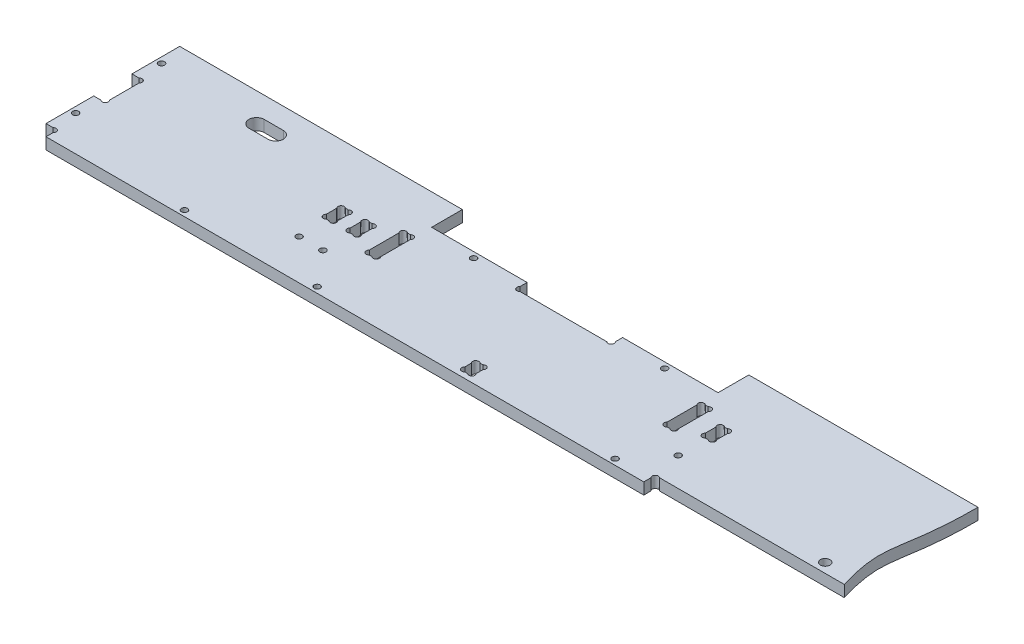
SolidWorks part; units mm, degrees
ref_plane "Plan de face" through (0, 0, 0) normal (0, 0, 1) x (1, 0, 0)
ref_plane "Plan de dessus" through (0, 0, 0) normal (0, 1, 0) x (1, 0, 0)
ref_plane "Plan de droite" through (0, 0, 0) normal (1, 0, 0) x (0, 0, -1)
sketch "Esquisse1" plane through (0, 0, 0) normal (0, 1, 0) x (1, 0, 0)
  line L0 (-13.419, 0) -> (480.5123, 0) construction
  line L1 (0, -21.3485) -> (0, 130.4665) construction
  line L2 (63.3362, 3) -> (427.6375, 3) construction
  line L3 (298, -66.9493) -> (298, 92.6945) construction
  line L4 (-13.419, 82) -> (480.5123, 82) construction
  line L5 (75.5, 6) -> (75.5, -21.3485) construction
  line L6 (457.6214, 41) -> (252.9914, 41) construction
  line L7 (300.2627, 51) -> (301.7373, 51)
  line L8 (142, 90.8171) -> (142, 7) construction
  line L9 (133, 90.8171) -> (133, -36.6843) construction
  line L10 (127, 90.8171) -> (127, 10) construction
  line L11 (109.7789, 46) -> (136.5161, 46) construction
  line L12 (-19.7637, 41) -> (137.7878, 41) construction
  line L13 (130, 28) -> (130, 5) construction
  line L14 (133, 46) -> (116.3933, 29.3933) construction
  line L15 (130.7373, 46) -> (129.2627, 46)
  line L16 (127, 43.7373) -> (127, 38.2627)
  line L17 (6, 31) -> (-11.5553, 48.5553) construction
  line L18 (6, 33.2627) -> (6, 48.7373)
  line L19 (3.7373, 31) -> (0, 31)
  line L20 (457.6214, 76) -> (-13.419, 76) construction
  line L21 (223, -7.7025) -> (223, 120.8663) construction
  line L22 (148, 59.9) -> (198, 59.9)
  line L23 (129.2627, 36) -> (130.7373, 36)
  line L24 (133, 38.2627) -> (133, 43.7373)
  line L25 (112.072, 21) -> (136.5161, 21) construction
  line L26 (313, 38.2627) -> (313, 43.7373)
  line L27 (304, -66.9493) -> (304, 92.6945) construction
  line L28 (266.0575, 31) -> (303.7284, 31) construction
  line L29 (301, -36.6843) -> (301, 28) construction
  line L30 (304, 31) -> (293.1513, 41.8487) construction
  line L31 (304, 33.2627) -> (304, 48.7373)
  line L32 (300.2627, 31) -> (301.7373, 31)
  line L33 (298, 33.2627) -> (298, 48.7373)
  line L34 (148, 33.2627) -> (148, 48.7373)
  line L35 (145.7373, 31) -> (144.2627, 31)
  line L36 (142, 33.2627) -> (142, 48.7373)
  line L37 (145.7373, 51) -> (144.2627, 51)
  line L38 (316.7373, 36) -> (315.2627, 36)
  line L39 (319, 43.7373) -> (319, 38.2627)
  line L40 (0, 51) -> (0, 76)
  line L41 (148, 59.9) -> (148, 76)
  line L42 (315.2627, 46) -> (316.7373, 46)
  line L43 (298, 59.9) -> (298, 76)
  line L44 (0, 31) -> (0, 6)
  line L45 (6, 0) -> (319, 0)
  line L46 (418, 130.4665) -> (418, -14.1262) construction
  line L47 (-13.419, 6) -> (435.2079, 6) construction
  line L48 (6, 6) -> (-8.187, -8.187) construction
  line L49 (6, 85.6538) -> (6, -21.3485) construction
  line L50 (3, 8.3351) -> (3, 24.8557) construction
  line L51 (-19.7637, 31) -> (14.2673, 31) construction
  line L52 (0, 6) -> (3.7373, 6)
  line L53 (6, 3.7373) -> (6, 0)
  line L54 (123.75, 56) -> (123.75, 36.4663) construction
  line L55 (144.2627, 59.9) -> (294, 59.9) construction
  line L56 (114.5, 38.2627) -> (114.5, 43.7373)
  line L57 (118.2373, 36) -> (116.7627, 36)
  line L58 (120.5, 43.7373) -> (120.5, 38.2627)
  line L59 (116.7627, 46) -> (118.2373, 46)
  line L60 (3.7373, 51) -> (0, 51)
  line L61 (-16.9102, 18.5) -> (9.1728, 18.5) construction
  line L62 (298, 76) -> (418, 76)
  line L63 (319, 50.248) -> (319, -8.187) construction
  line L64 (319, 0) -> (319, 3.7373)
  line L65 (321.2627, 6) -> (418, 6)
  line L66 (421.2069, 11) -> (397.2621, 11) construction
  line L67 (319, 6) -> (339.0526, -14.0526) construction
  line L68 (148, 76) -> (0, 76)
  line L69 (248, 70.2137) -> (248, 48.7373) construction
  line L70 (248.9026, 53.9) -> (182.039, 53.9) construction
  line L71 (284.2388, 56.9) -> (266.0575, 56.9) construction
  line L72 (273, 70.2137) -> (273, 48.7373) construction
  line L73 (248, 53.9) -> (234.5843, 67.3157) construction
  line L74 (198, 56.1627) -> (198, 59.9)
  line L75 (200.2627, 53.9) -> (245.7373, 53.9)
  line L76 (248, 56.1627) -> (248, 59.9)
  line L77 (248, 59.9) -> (298, 59.9)
  line L78 (450.6248, 52) -> (401.2893, 52) construction
  line L79 (433.9487, 26) -> (401.2893, 26) construction
  line L80 (403, -7.7025) -> (403, 15.4615) construction
  line L81 (414, 38.2627) -> (414, 17) construction
  line L82 (-13.419, 61) -> (105.3056, 61) construction
  line L83 (60.25, 90.8171) -> (60.25, 53.9) construction
  line L84 (51.487, 65) -> (97.3487, 65) construction
  line L85 (51.487, 57) -> (97.3487, 57) construction
  line L86 (65.25, 53.9) -> (65.25, 90.8171) construction
  line L87 (55.25, 65) -> (65.25, 65)
  line L88 (55.25, 57) -> (65.25, 57)
  line L89 (220, 3) -> (231.7512, 14.7512) construction
  line L90 (220, -7.7025) -> (220, 21) construction
  line L91 (212.4838, 7) -> (225.5521, 7) construction
  line L92 (220, 8.7373) -> (220, 5.2627)
  line L93 (222.2627, 3) -> (223.7373, 3)
  line L94 (222.2627, 11) -> (223.7373, 11)
  line L95 (226, 5.2627) -> (226, 8.7373)
  circle A0 centre (75.5, 3) radius 1.6
  arc A1 (301.7373, 51) -> (304, 48.7373) centre (302.8686, 49.8686) cw
  arc A2 (300.2627, 51) -> (298, 48.7373) centre (299.1314, 49.8686) ccw
  arc A3 (133, 43.7373) -> (130.7373, 46) centre (131.8686, 44.8686) ccw
  arc A4 (127, 43.7373) -> (129.2627, 46) centre (128.1314, 44.8686) cw
  arc A5 (133, 38.2627) -> (130.7373, 36) centre (131.8686, 37.1314) cw
  arc A6 (3.7373, 31) -> (6, 33.2627) centre (4.8686, 32.1314) ccw
  arc A7 (3.7373, 51) -> (6, 48.7373) centre (4.8686, 49.8686) cw
  circle A8 centre (3, 63.5) radius 1.6
  circle A9 centre (3, 18.5) radius 1.6
  arc A10 (127, 38.2627) -> (129.2627, 36) centre (128.1314, 37.1314) ccw
  circle A11 centre (130, 21) radius 1.6
  arc A12 (301.7373, 31) -> (304, 33.2627) centre (302.8686, 32.1314) ccw
  arc A13 (300.2627, 31) -> (298, 33.2627) centre (299.1314, 32.1314) cw
  circle A14 centre (145, 3) radius 1.6
  arc A15 (145.7373, 31) -> (148, 33.2627) centre (146.8686, 32.1314) ccw
  arc A16 (144.2627, 31) -> (142, 33.2627) centre (143.1314, 32.1314) cw
  circle A17 centre (301, 3) radius 1.6
  circle A18 centre (316, 21) radius 1.6
  arc A19 (319, 38.2627) -> (316.7373, 36) centre (317.8686, 37.1314) cw
  arc A20 (313, 38.2627) -> (315.2627, 36) centre (314.1314, 37.1314) ccw
  arc A21 (319, 43.7373) -> (316.7373, 46) centre (317.8686, 44.8686) ccw
  arc A22 (313, 43.7373) -> (315.2627, 46) centre (314.1314, 44.8686) cw
  circle A23 centre (117.5, 21) radius 1.6
  arc A24 (6, 3.7373) -> (3.7373, 6) centre (4.8686, 4.8686) ccw
  arc A25 (120.5, 38.2627) -> (118.2373, 36) centre (119.3686, 37.1314) cw
  arc A26 (114.5, 38.2627) -> (116.7627, 36) centre (115.6314, 37.1314) ccw
  arc A27 (120.5, 43.7373) -> (118.2373, 46) centre (119.3686, 44.8686) ccw
  arc A28 (114.5, 43.7373) -> (116.7627, 46) centre (115.6314, 44.8686) cw
  arc A29 (145.7373, 51) -> (148, 48.7373) centre (146.8686, 49.8686) cw
  arc A30 (144.2627, 51) -> (142, 48.7373) centre (143.1314, 49.8686) ccw
  arc A31 (321.2627, 6) -> (319, 3.7373) centre (320.1314, 4.8686) ccw
  circle A32 centre (273, 56.9) radius 1.6
  arc A33 (245.7373, 53.9) -> (248, 56.1627) centre (246.8686, 55.0314) ccw
  circle A34 centre (173, 56.9) radius 1.6
  arc A35 (200.2627, 53.9) -> (198, 56.1627) centre (199.1314, 55.0314) cw
  arc A36 (65.25, 57) -> (65.25, 65) centre (65.25, 61) ccw
  arc A37 (55.25, 57) -> (55.25, 65) centre (55.25, 61) cw
  circle A38 centre (403, 11) radius 2.5
  arc A39 (220, 5.2627) -> (222.2627, 3) centre (221.1314, 4.1314) ccw
  arc A40 (226, 5.2627) -> (223.7373, 3) centre (224.8686, 4.1314) cw
  arc A41 (226, 8.7373) -> (223.7373, 11) centre (224.8686, 9.8686) ccw
  arc A42 (220, 8.7373) -> (222.2627, 11) centre (221.1314, 9.8686) cw
  spline S0 degree 3 poles (418, 76) (417.9833, 33.7949) (408.8808, 36.4699) (418, 6) knots 0 0 0 0 1 1 1 1
  dimension "D17" = 3
  dimension "D18" = 45
  dimension "D10" = 6
  dimension "D12" = 6
  dimension "D11" = 9
  dimension "D16" = 6
  dimension "D20" = 16.1
  dimension "D21" = 45
  dimension "D27" = 20
  dimension "D9" = 10
  dimension "D28" = 3.25
  dimension "D30" = 12.5
  dimension "D31" = 25
  dimension "D36" = 24
  dimension "D44" = 4
  dimension "D38" = 5
  dimension "D45" = 15
  dimension "D46" = 4
  dimension "D2" = 82
  dimension "D3" = 75
  dimension "D4" = 41
  dimension "D5" = 120
  dimension "D6" = 223
  dimension "D7" = 3
  dimension "D8" = 69.5
  dimension "D13" = 3
  dimension "D14" = 5
  dimension "D15" = 30
  dimension "D19" = 45
  dimension "D22" = 6
  dimension "D23" = 6
  dimension "D24" = 3
  dimension "D25" = 10
  dimension "D26" = 45
  dimension "D29" = 45
  dimension "D32" = 25
  dimension "D33" = 3
  dimension "D34" = 6
  dimension "D35" = 45
  dimension "D37" = 20
  dimension "D39" = 4
  dimension "D40" = 54.25
  dimension "D41" = 15
  dimension "D42" = 5
  dimension "D43" = 4
  dimension "D47" = 3
  dimension "D48" = 45
extrude "Boss.-Extru.1" add sketch "Esquisse1" along normal blind 6
